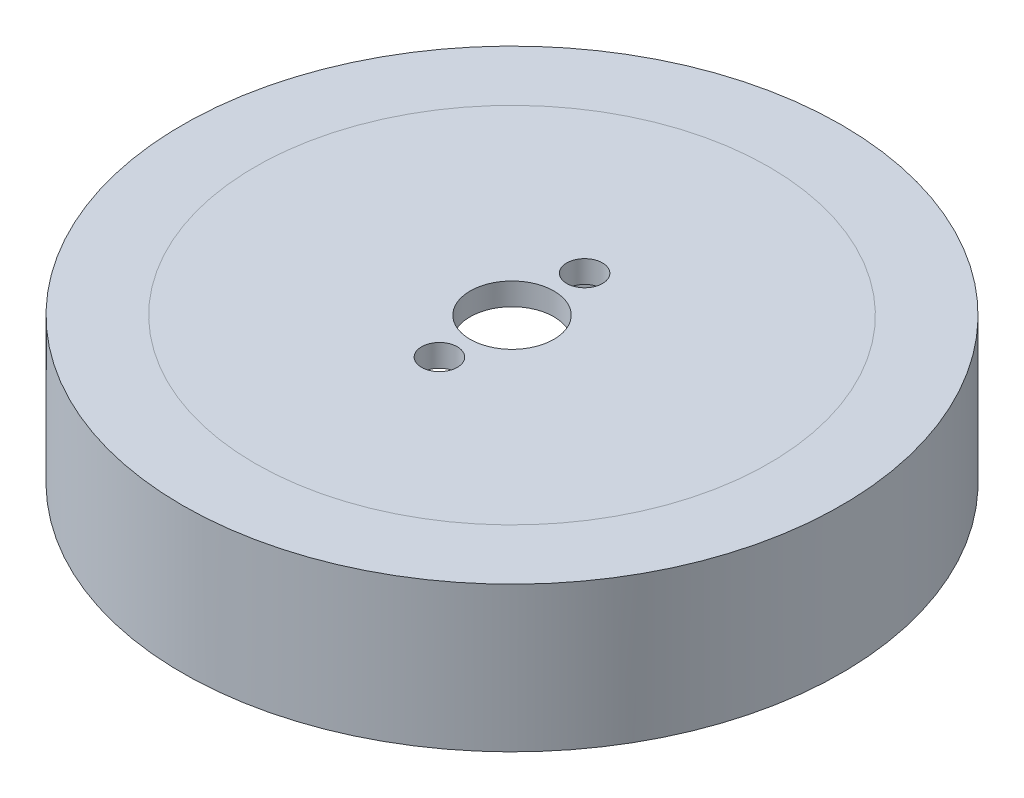
SolidWorks part; units mm, degrees
material "6061 合金"
ref_plane "前视基准面" through (0, 0, 0) normal (0, 0, 1) x (1, 0, 0)
ref_plane "上视基准面" through (0, 0, 0) normal (0, 1, 0) x (1, 0, 0)
ref_plane "右视基准面" through (0, 0, 0) normal (1, 0, 0) x (0, 0, -1)
sketch "草图1" plane through (0, 0, 0) normal (0, 1, 0) x (1, 0, 0)
  circle A0 centre (0, 0) radius 23
  circle A1 centre (0, 0) radius 6.5 construction
  circle A3 centre (0, 6.5) radius 1.6
  circle A11 centre (0, -6.5) radius 1.6
  circle A13 centre (0, 0) radius 3.75
  point P15 (0, 0)
  dimension "D1" = 46
  dimension "D2" = 13
  dimension "D3" = 3.2
  dimension "D4" = 7.5
extrude "凸台-拉伸1" add sketch "草图1" along normal blind 13
sketch "草图3" plane through (0, 0, 0) normal (0, -1, 0) x (1, 0, 0)
  circle A0 centre (0, 0) radius 21
  dimension "D1" = 42
extrude "切除-拉伸1" cut sketch "草图3" against normal blind 11
sketch "草图4" plane through (0, 0, 0) normal (0, -1, 0) x (1, 0, 0)
  circle A0 centre (0, 0) radius 29.5
  circle A1 centre (0, 0) radius 23 construction
  circle A2 centre (0, 0) radius 23
  dimension "D1" = 59
extrude "凸台-拉伸2" add sketch "草图4" against normal up to surface (13 mm away) separate body up to face at (0, 13, 8.1)
